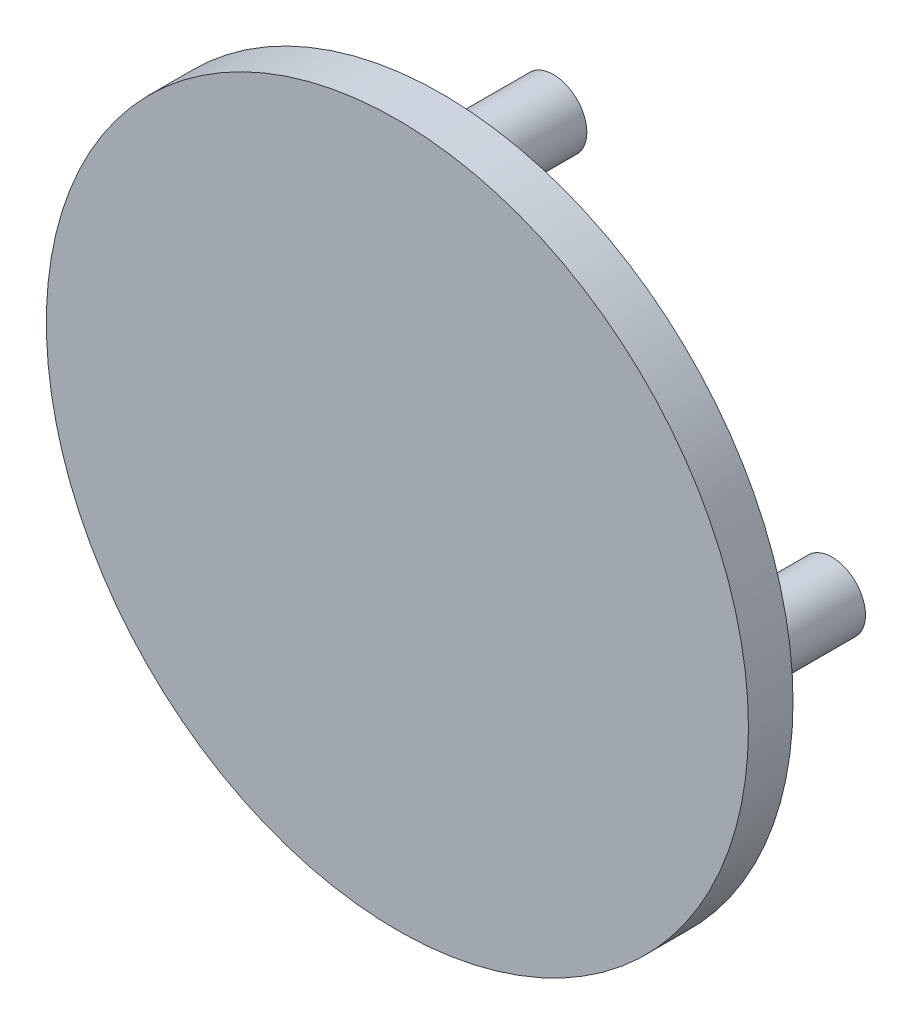
SolidWorks part; units mm, degrees
ref_plane "Front Plane" through (0, 0, 0) normal (0, 0, 1) x (1, 0, 0)
ref_plane "Top Plane" through (0, 0, 0) normal (0, 1, 0) x (1, 0, 0)
ref_plane "Right Plane" through (0, 0, 0) normal (1, 0, 0) x (0, 0, -1)
sketch "Sketch1" plane through (0, 0, 0) normal (0, 0, 1) x (1, 0, 0)
  circle A0 centre (0, 0) radius 25
  dimension "D1" = 50
extrude "Boss-Extrude1" add sketch "Sketch1" along normal blind 8 contours A0
sketch "Sketch2" plane through (0, 0, 8) normal (0, 0, 1) x (1, 0, 0)
  circle A0 centre (0, 0) radius 63
  dimension "D1" = 126
extrude "Boss-Extrude2" add sketch "Sketch2" along normal blind 8
sketch "Sketch3" plane through (0, 0, 8) normal (0, 0, -1) x (-1, 0, 0)
  circle A0 centre (0, 0) radius 50
  dimension "D1" = 100
sketch "Sketch4" plane through (0, 0, 8) normal (0, 0, -1) x (-1, 0, 0)
  circle A0 centre (0, 50) radius 6
  circle A1 centre (50, 0) radius 6
  circle A2 centre (0, -50) radius 6
  circle A3 centre (-50, 0) radius 6
  point P12 (0, 0)
  dimension "D1" = 12
  dimension "D2" = 50
  dimension "D3" = 4
extrude "Boss-Extrude3" add sketch "Sketch4" along normal blind 20
